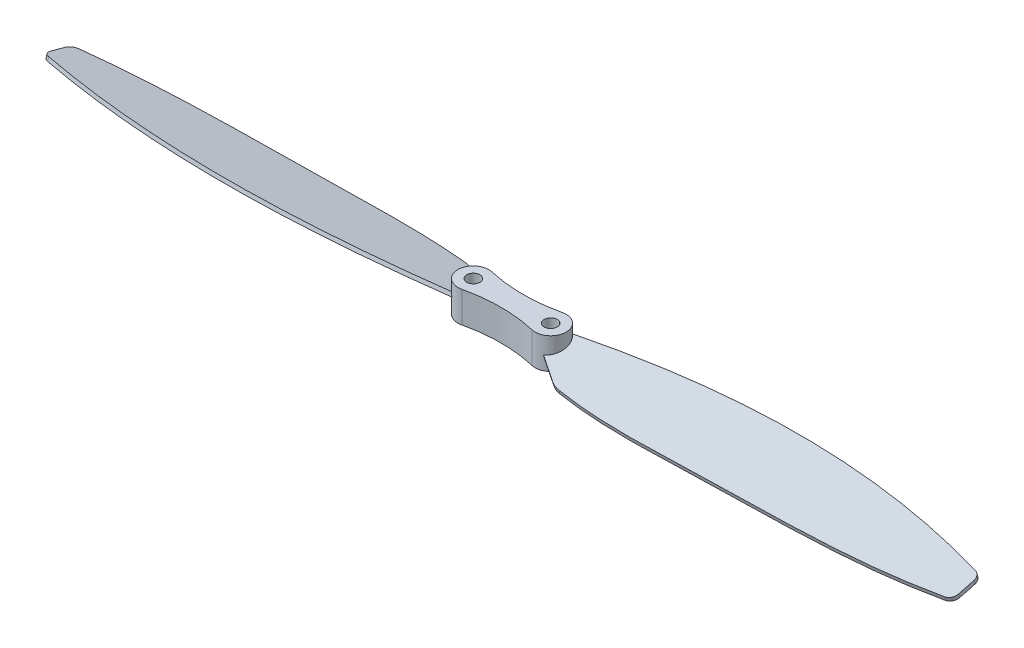
SolidWorks part; units mm, degrees
ref_plane "前视基准面" through (0, 0, 0) normal (0, 0, 1) x (1, 0, 0)
ref_plane "上视基准面" through (0, 0, 0) normal (0, 1, 0) x (1, 0, 0)
ref_plane "右视基准面" through (0, 0, 0) normal (1, 0, 0) x (0, 0, -1)
other "Configuration Table"
sketch "草图1" plane through (0, 0, 0) normal (0, 1, 0) x (1, 0, 0)
  line L0 (-5, 0) -> (5, 0)
  circle A0 centre (5, 0) radius 2
  circle A1 centre (-5, 0) radius 2
  arc A2 (-4.5455, 1.9477) -> (4.5455, 1.9477) centre (0, 21.4243) ccw
  arc A3 (-4.5455, -1.9477) -> (4.5455, -1.9477) centre (0, -21.4243) cw
  point P4 (0, 0)
  dimension "D1" = 4
  dimension "D2" = 4
extrude "凸台-拉伸1" add sketch "草图1" along normal blind 4
sketch "草图2" plane through (0, 0, 0) normal (1, 0, 0) x (0, 0, -1)
  line L3 (-2, 1.4641) -> (2, 2.5359)
  line L4 (2, 0) -> (2, 4) construction
  point P7 (0, 2)
ref_plane "基准面1" through (0, 1.866, 0.5) normal (0, -0.9659, -0.2588) x (0, 0.2588, -0.9659)
sketch "草图3" plane through (0, 1.866, 0.5) normal (0, -0.9659, -0.2588) x (0, 0.2588, -0.9659)
  line L0 (-0.721, 5) -> (-3.2442, 8.9638)
  line L1 (-0.721, 5) -> (1.9319, 5)
  arc A0 (0.8564, 59.4938) -> (-1.2492, 59.4869) centre (0, 0) ccw
  arc A1 (1.8115, 58.7391) -> (0.8564, 59.4938) centre (0.842, 58.4939) ccw
  arc A2 (-2.214, 58.6549) -> (-1.2492, 59.4869) centre (-1.2282, 58.4871) cw
  arc A3 (-3.2442, 8.9638) -> (-3.6862, 10.1722) centre (-0.7134, 10.5748) cw
  ellipse E0 centre (0, 5) end of major axis (0, 7) minor radius 1.9319 (1.8813, 4.5455) -> (-1.8813, 4.5455) ccw construction
  spline S0 degree 3 poles (1.9319, 5) (5.58, 23.0552) (6.3567, 40.7679) (1.8115, 58.7391) knots 0 0 0 0 0.986483 0.986483 0.986483 0.986483
  spline S1 degree 3 poles (-3.6862, 10.1722) (-4.5254, 16.3692) (-3.6951, 32.2616) (-4.0028, 48.1455) (-2.214, 58.6549) knots 0.016611 0.016611 0.016611 0.016611 0.37464 0.984356 0.984356 0.984356 0.984356
  dimension "D1" = 119
  dimension "D2" = 1
  dimension "D3" = 3
extrude "凸台-拉伸2" add sketch "草图3" along normal mid plane 0.5
ref_axis "基准轴1" through (0, 4.2, 0) along (0, -1, 0)
pattern_circular "阵列(圆周)1" count 2 over 360 about axis through (0, 4.2, 0) along (0, -1, 0) of "凸台-拉伸2"
sketch "草图4" plane through (0, 4, 0) normal (0, 1, 0) x (1, 0, 0)
  circle A0 centre (-5, 0) radius 0.85
  circle A1 centre (5, 0) radius 0.85
  dimension "D1" = 1.7
  dimension "D2" = 1.7
extrude "切除-拉伸1" cut sketch "草图4" against normal through all
